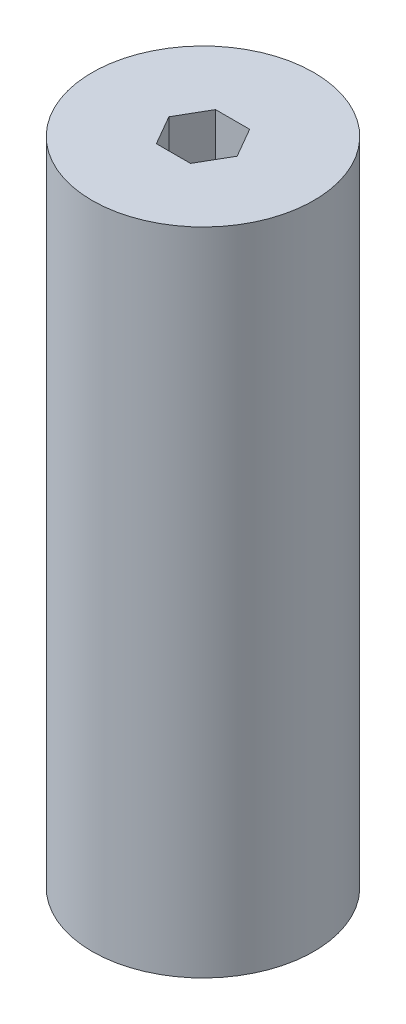
SolidWorks part; units mm, degrees
ref_plane "Front Plane" through (0, 0, 0) normal (0, 0, 1) x (1, 0, 0)
ref_plane "Top Plane" through (0, 0, 0) normal (0, 1, 0) x (1, 0, 0)
ref_plane "Right Plane" through (0, 0, 0) normal (1, 0, 0) x (0, 0, -1)
sketch "Sketch1" plane through (0, 0, 0) normal (0, 1, 0) x (1, 0, 0)
  line L1 (3.6662, -6.35) -> (7.3323, 0)
  line L2 (7.3323, 0) -> (3.6662, 6.35)
  line L3 (3.6662, 6.35) -> (-3.6662, 6.35)
  line L4 (-3.6662, 6.35) -> (-7.3323, 0)
  line L5 (-7.3323, 0) -> (-3.6662, -6.35)
  line L6 (-3.6662, -6.35) -> (3.6662, -6.35)
  circle A0 centre (0, 0) radius 23.8125
  circle A1 centre (0, 0) radius 6.35 construction
  dimension "D1" = 12.7
  dimension "D2" = 47.625
extrude "Boss-Extrude1" add sketch "Sketch1" along normal blind 139.7
